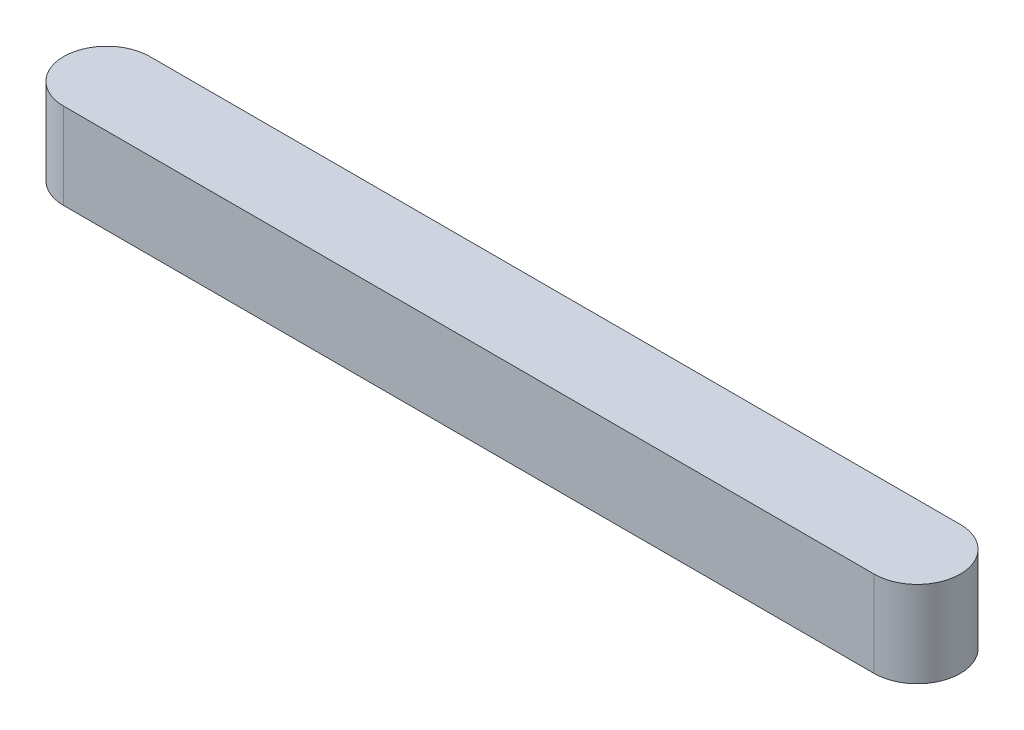
SolidWorks part; units mm, degrees
ref_plane "Front Plane" through (0, 0, 0) normal (0, 0, 1) x (1, 0, 0)
ref_plane "Top Plane" through (0, 0, 0) normal (0, 1, 0) x (1, 0, 0)
ref_plane "Right Plane" through (0, 0, 0) normal (1, 0, 0) x (0, 0, -1)
sketch "Sketch1" plane through (0, 0, 0) normal (0, 1, 0) x (1, 0, 0)
  line L0 (-62.5, 0) -> (62.5, 0) construction
  line L1 (-56.5, 0) -> (56.5, 0) construction
  line L2 (-56.5, 6) -> (56.5, 6)
  line L3 (-56.5, -6) -> (56.5, -6)
  arc A0 (-56.5, 6) -> (-56.5, -6) centre (-56.5, 0) ccw
  arc A1 (56.5, -6) -> (56.5, 6) centre (56.5, 0) ccw
  point P4 (0, 0)
  point P7 (0, 0)
  point P12 (0, 0)
  point P13 (0, 0)
  point P14 (0, 0)
  point P15 (0, 0)
  dimension "D" = 6
  dimension "L" = 125
extrude "Boss-Extrude1" add sketch "Sketch1" along normal blind 12
sketch "Sketch2" plane through (0, 12, 0) normal (0, 1, 0) x (1, 0, 0)
  line L0 (56.5, 6) -> (-56.5, 6) construction
  line L1 (0, 6) -> (62.5, 6)
  line L2 (0, 6) -> (0, -6)
  line L3 (0, -6) -> (62.5, -6)
  line L4 (62.5, 6) -> (62.5, -6)
  line L5 (-56.5, -6) -> (56.5, -6) construction
  arc A0 (56.5, -6) -> (56.5, 6) centre (56.5, 0) ccw construction
  point P6 (0, 0)
extrude "Cut-Extrude1" [suppressed] cut sketch "Sketch2" against normal through all
equation "\"L\" = 125"
equation "\"D\" = 6"
equation "\"H\" = 12"
equation "\"Cut-Extrude1\"= IIF ( \"L\" = 160 , \"unsuppressed\" , IIF ( \"L\" = 100 , \"unsuppressed\" , \"suppressed\" ) )"
equation "\"L@Sketch1\"=\"L\""
equation "\"D@Sketch1\"=\"D\""
equation "\"H@Boss-Extrude1\"=\"H\""
